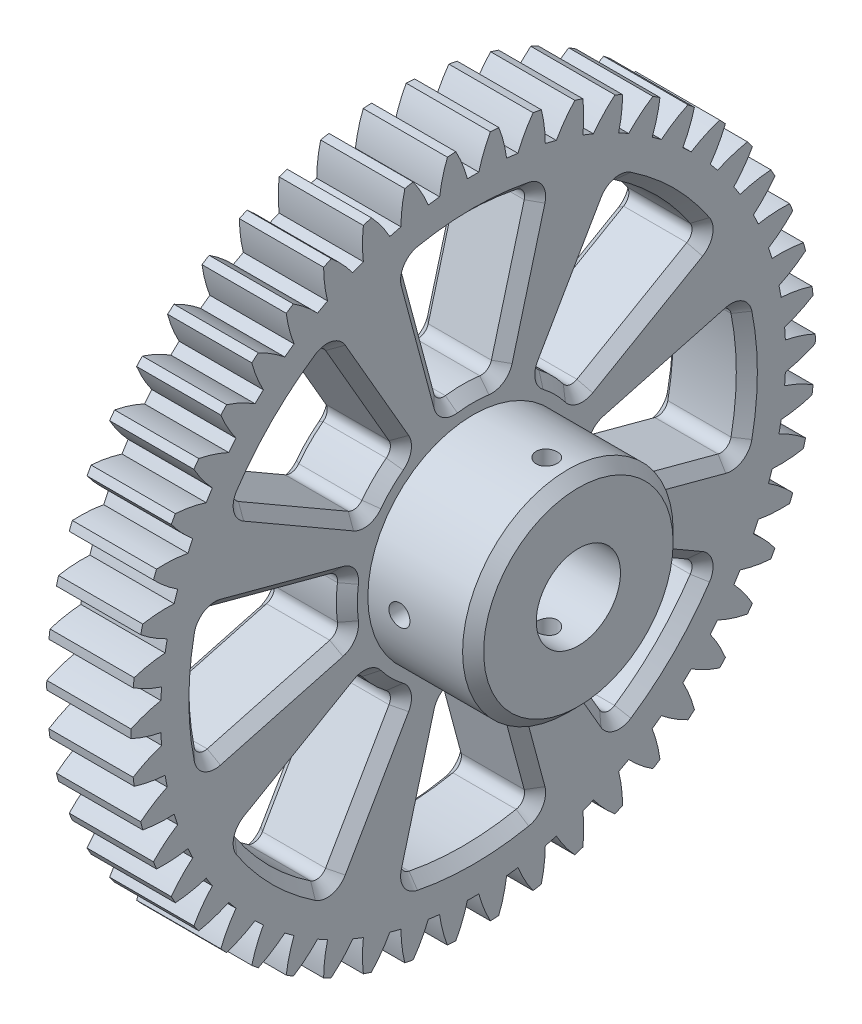
SolidWorks part; units mm, degrees
material "ПК/АБС"
ref_plane "Plane1" through (0, 0, 0) normal (0, 0, 1) x (1, 0, 0)
ref_plane "Plane2" through (0, 0, 0) normal (0, 1, 0) x (1, 0, 0)
ref_plane "Plane3" through (0, 0, 0) normal (1, 0, 0) x (0, 0, -1)
sketch "HoldingSke" plane through (0, 0, 0) normal (0, 1, 0) x (1, 0, 0)
  line L0 (0, 0) -> (0.5142, -0.6128)
  line L1 (-15, 0) -> (100, 0) construction
  line L2 (0, 0) -> (-2.1039, 2.3779)
  line L3 (0, 0) -> (-11.863, 4.5341)
  line L4 (0, 0) -> (5.5511, 6.6156)
  line L5 (0, 0) -> (-46.8476, -17.4728)
  line L6 (0, 0) -> (-6.6317, -4.4744)
  line L7 (-2.1039, 2.3779) -> (8.6587, 51.2063)
  line L8 (-76.2, 54.61) -> (-74.8, 54.61)
  line L9 (-71.009, 38.7566) -> (-53.1078, 45.2721)
  line L10 (-76.2, 71.12) -> (104.1128, 71.12)
  line L11 (0, 0) -> (-8, 0)
  line L12 (-76.2, 101.6) -> (-76.155, 101.6)
  line L13 (24.9733, 27.94) -> (52.9518, 28.4284)
  line L14 (24.9733, 27.94) -> (24.9743, 27.94)
  line L15 (24.9733, 27.94) -> (100.4006, 29.5858)
  line L16 (-63.627, -1.25) -> (-12.827, -1.25)
  circle A0 centre (0, 0) radius 4
  circle A1 centre (0, 0) radius 29.6865
  circle A2 centre (0, 0) radius 37.5
  circle A3 centre (0, 0) radius 4
  dimension "MHD" = 59.373
  dimension "Hub_dia" = 75
  dimension "Bore" = 8
  dimension "MBD" = 8
  dimension "Num_teeth" = 50
  dimension "Pitch" = 0.8
  dimension "Overall_len" = 50
  dimension "Show_teeth" = 50
  dimension "Thickness" = 8
  dimension "OAL" = 50.0005
  dimension "T_dim" = 1.4
  dimension "Ap" = 20
  dimension "H" = 19.05
  dimension "Pitch_radius" = 180.3128
  dimension "Width" = 8
  dimension "Backlash" = 0.045
  dimension "Addendum_fac" = 1
  dimension "Dedendum_fac" = 1.25
  dimension "Clearance_fac" = 0.25
  dimension "Dedendum_add" = 0.001
  dimension "Module" = 1.25
sketch "BasProSke" plane through (0, 0, 0) normal (0, 1, 0) x (1, 0, 0)
  line L0 (-10, 0) -> (60, 0) construction
  line L1 (0, 0) -> (0, 32.5)
  line L2 (0, 0) -> (8, 0)
  line L3 (8, 0) -> (8, 32.5)
  line L4 (8, 32.5) -> (0, 32.5)
  dimension "Thickness" = 8
  dimension "Diameter" = 65
revolve "Base-Revolve" add sketch "BasProSke" angle 360 about L0
sketch "TooCutSke" plane through (0, 0, 0) normal (1, 0, 0) x (0, 0, -1)
  line L1 (0, 0) -> (0, 107) construction
  line L2 (0, 0) -> (-1.0603, 31.232) construction
  line L3 (0, 0) -> (-3.9228, 62.3506) construction
  line L4 (-1.0603, 31.232) -> (-1.9614, 31.1753) construction
  arc A0 (0.543, 29.6815) -> (-0.543, 29.6815) centre (0, 0) ccw
  arc A1 (1.6539, 32.4833) -> (-1.6539, 32.4833) centre (0, 0) ccw
  circle A2 centre (0, 0) radius 31.25 construction
  circle A3 centre (0, 0) radius 29.3654 construction
  arc A4 (-0.543, 29.6815) -> (-1.6539, 32.4833) centre (-12.6336, 26.5088) ccw
  arc A5 (1.6539, 32.4833) -> (0.543, 29.6815) centre (12.6336, 26.5088) ccw
  dimension "Root_dia" = 59.373
  dimension "Overcut_dia" = 65.0508
  dimension "Pitch_dia" = 62.5
  dimension "Base_dia" = 58.7308
  dimension "Flank_rad" = 12.5
  dimension "Half_ang" = 3.6
  dimension "Half_CT" = 0.9028
extrude "ToothCut" cut sketch "TooCutSke" along normal through all
fillet "Breaks" [suppressed] radius 0.025
fillet "RootFillets" [suppressed] radius 0.3135
pattern_circular "TeethCuts" count 50 every 7.2 about axis through (-10, 0, 0) along (1, 0, 0) of "ToothCut", "RootFillets", "Breaks"
sketch "HubNeaOneSke" plane through (0, 0, 0) normal (-1, 0, 0) x (0, 0, 1)
  circle A0 centre (0, 0) radius 29.6865
  dimension "Diameter" = 59.373
extrude "HubNearOne" [suppressed] add sketch "HubNeaOneSke" along normal blind 42.0005
sketch "HubNeaBotSke" plane through (0, 0, 0) normal (-1, 0, 0) x (0, 0, 1)
  circle A0 centre (0, 0) radius 29.6865
  dimension "Diameter" = 59.373
extrude "HubNearBoth" [suppressed] add sketch "HubNeaBotSke" along normal blind 21.0002
ref_plane "FarPln" through (8, 0, 0) normal (1, 0, 0) x (0, 0, -1)
sketch "HubFarSke" plane through (8, 0, 0) normal (1, 0, 0) x (0, 0, -1)
  circle A0 centre (0, 0) radius 29.6865
  dimension "Diameter" = 59.373
extrude "HubFar" [suppressed] add sketch "HubFarSke" along normal blind 21.0002
sketch "BorSke" plane through (0, 0, 0) normal (1, 0, 0) x (0, 0, -1)
  circle A0 centre (0, 0) radius 4
  dimension "Diameter" = 8
extrude "Bore" cut sketch "BorSke" along normal mid plane 100.0009
sketch "KeySke" plane through (0, 0, 0) normal (1, 0, 0) x (0, 0, -1)
  line L0 (-1.5, 0) -> (-1.5, 5.4)
  line L1 (-1.5, 5.4) -> (1.5, 5.4)
  line L2 (1.5, 5.4) -> (1.5, 0)
  line L3 (0, 0) -> (0, 34) construction
  line L4 (-1.5, 0) -> (1.5, 0)
  dimension "Offset" = 5.4
  dimension "Width" = 3
extrude "Keyway" [suppressed] cut sketch "KeySke" along normal mid plane 100.0009
pattern_circular "Keyway2" [suppressed] count 2 every 90 about axis through (-10, 0, 0) along (1, 0, 0)
sketch "Эскиз1" plane through (8, 0, 0) normal (1, 0, 0) x (0, 0, -1)
  circle A0 centre (0, 0) radius 4 construction
  circle A1 centre (0, 0) radius 4
  circle A2 centre (0, 0) radius 10
  dimension "D1" = 20
extrude "Бобышка-Вытянуть1" add sketch "Эскиз1" along normal blind 10
sketch "Эскиз2" plane through (0, 0, 0) normal (0, 1, 0) x (1, 0, 0)
  line L0 (18, -10) -> (18, 10) construction
  line L1 (18, -10) -> (18, 10)
  line L2 (8, -10) -> (8, 10) construction
  line L3 (8, -10) -> (8, 10)
  line L4 (18, 0) -> (8, 0) construction
  circle A0 centre (15, 0) radius 1
  dimension "D1" = 2
  dimension "D2" = 3
extrude "Вырез-Вытянуть1" cut sketch "Эскиз2" against normal through all both and the other way through all contours A0 L4 | L4 A0
sketch "Эскиз3" plane through (0, 0, 0) normal (0, 0, 1) x (1, 0, 0)
  line L0 (18, -10) -> (18, 10) construction
  line L1 (18, -10) -> (18, 10)
  line L2 (8, -10) -> (8, 10) construction
  line L3 (8, -10) -> (8, 10)
  line L4 (18, 0) -> (8, 0) construction
  circle A0 centre (11, 0) radius 1
  dimension "D1" = 2
  dimension "D2" = 3
extrude "Вырез-Вытянуть2" cut sketch "Эскиз3" against normal through all both and the other way through all contours L4 A0 | A0 L4
chamfer "Фаска1" distance 1 angle 45 1 edges at (18, 0, -10)
chamfer "Фаска2" distance 1 angle 45 1 edges at (0, 0, -4)
sketch "Эскиз4" plane through (8, 0, 0) normal (1, 0, 0) x (0, 0, -1)
  line L0 (-39.9819, 0) -> (39.9819, 0) construction
  line L1 (-11.7367, -2.5) -> (-25.2681, -6.1257)
  line L2 (-11.7367, 2.5) -> (-25.2681, 6.1257)
  circle A0 centre (0, 0) radius 10 construction
  circle A1 centre (0, 0) radius 10
  circle A2 centre (0, 0) radius 12
  circle A3 centre (0, 0) radius 26
  dimension "D1" = 52
  dimension "D2" = 24
  dimension "D3" = 30
  dimension "D4" = 5
extrude "Вырез-Вытянуть3" cut sketch "Эскиз4" against normal through all both and the other way through all contours A3 L0 A2 L2 | L0 A3 L1 A2
fillet "Скругление1" radius 1 4 edges at (4, 2.5, 11.7367) (4, -2.5, 11.7367) (4, 6.1257, 25.2681) (4, -6.1257, 25.2681)
chamfer "Фаска3" distance 1 angle 45 16 edges at (0, -4.2959, 18.4392) (0, -2.3239, 12.0458) (0, -5.7386, 25.0451) (0, 0, 12) (0, 0, 26) (0, 2.3239, 12.0458) (0, 5.7386, 25.0451) (0, 4.2959, 18.4392) (8, 0, 12) (8, -2.3239, 12.0458) (8, 2.3239, 12.0458) (8, -4.2959, 18.4392) (8, 4.2959, 18.4392) (8, -5.7386, 25.0451) (8, 5.7386, 25.0451) (8, 0, 26)
pattern_circular "Круговой массив1" count 8 every 45 about axis through (0, 0, 0) along (1, 0, 0) of "Вырез-Вытянуть3", "Скругление1", "Фаска3"
equation "' \"Module@HoldingSke\" = 6.35"
equation "' \"Num_teeth@HoldingSke\" = 12"
equation "' \"Ap@HoldingSke\" =  20"
equation "' \"Ap@HoldingSke\" = 20"
equation "' \"Width@HoldingSke\" = 0.5 * 25.4"
equation "' \"Hub_dia@HoldingSke\"= 1 * 25.4"
equation "' \"Hub_dia@HoldingSke\" = 1 * 25.4"
equation "' \"Overall_len@HoldingSke\" = 1.0 * 25.4"
equation "' \"Bore@HoldingSke\" = 0.75 * 25.4"
equation "' \"T_dim@HoldingSke\" = 0.1 * 25.4"
equation "' \"Width@KeySke\" = 0.25 * 25.4"
equation "' \"Show_teeth@HoldingSke\" = 13"
equation "' \"Backlash@HoldingSke\" = 0.009 * 25.4"
equation "' \"Addendum_fac@HoldingSke\" = 1.0"
equation "' \"Dedendum_fac@HoldingSke\" = 1.25"
equation "' \"Dedendum_add@HoldingSke\" = 0.00005 * 25.4"
equation "' \"Clearance_fac@HoldingSke\" = 0.25"
equation "\"Pitch@HoldingSke\" = 1 / \"Module@HoldingSke\""
equation "\"Overcut_dia@TooCutSke\" = (\"Num_teeth@HoldingSke\" + 2 * \"Addendum_fac@HoldingSke\") / \"Pitch@HoldingSke\" + 0.002 * 25.4"
equation "\"Pitch_dia@TooCutSke\" = \"Num_teeth@HoldingSke\" / \"Pitch@HoldingSke\""
equation "\"Base_dia@TooCutSke\" = \"Num_teeth@HoldingSke\" / \"Pitch@HoldingSke\" * cos((\"Ap@HoldingSke\"  * 3.14159265 / 180))"
equation "\"Root_dia@TooCutSke\" = (\"Num_teeth@HoldingSke\" + 2) / \"Pitch@HoldingSke\" - 2 * (\"Addendum_fac@HoldingSke\" + \"Dedendum_fac@HoldingSke\") / \"Pitch@HoldingSke\" - \"Dedendum_add@HoldingSke\" * 2"
equation "\"Half_ang@TooCutSke\" = 180 / \"Num_teeth@HoldingSke\""
equation "\"Half_CT@TooCutSke\" = \"Num_teeth@HoldingSke\" / \"Pitch@HoldingSke\" * sin((3.14159265 / 2 / \"Num_teeth@HoldingSke\")) / 2 - 7 * \"Backlash@HoldingSke\" / 4"
equation "\"Flank_rad@TooCutSke\" = \"Num_teeth@HoldingSke\" / \"Pitch@HoldingSke\" / 5"
equation "\"Radius@RootFillets\" = \"Clearance_fac@HoldingSke\" / \"Pitch@HoldingSke\" + \"Dedendum_add@HoldingSke\""
equation "\"Break_rad@Breaks\" = 0.02 / \"Pitch@HoldingSke\""
equation "\"Thickness@HoldingSke\" = \"Width@HoldingSke\""
equation "\"OAL@HoldingSke\" = \"Thickness@HoldingSke\""
equation "\"MHD@HoldingSke\" = (\"Num_teeth@HoldingSke\" + 2) / \"Pitch@HoldingSke\" - 2 * (\"Addendum_fac@HoldingSke\" + \"Dedendum_fac@HoldingSke\")  / \"Pitch@HoldingSke\" - \"Dedendum_add@HoldingSke\" * 2"
equation "\"MBD@HoldingSke\" = (\"Num_teeth@HoldingSke\" + 2) / \"Pitch@HoldingSke\" - 2 * (\"Addendum_fac@HoldingSke\" + \"Dedendum_fac@HoldingSke\")  / \"Pitch@HoldingSke\" - \"Dedendum_add@HoldingSke\" * 2 - 0.002 * 25.4"
equation "\"MHD@HoldingSke\" = ((sgn( \"MHD@HoldingSke\" - \"Hub_dia@HoldingSke\" )-1)*( \"MHD@HoldingSke\" - \"Hub_dia@HoldingSke\" ))/-2+ \"Hub_dia@HoldingSke\""
equation "\"MBD@HoldingSke\" = ((sgn( \"MBD@HoldingSke\" - \"Bore@HoldingSke\" )-1)*( \"MBD@HoldingSke\" - \"Bore@HoldingSke\" ))/-2+ \"Bore@HoldingSke\""
equation "\"OAL@HoldingSke\" = ((sgn( \"OAL@HoldingSke\" - \"Overall_len@HoldingSke\" )+1)*( \"OAL@HoldingSke\" - \"Overall_len@HoldingSke\" ))/2 + \"Overall_len@HoldingSke\" + 0.000002 * 25.4"
equation "\"Num_teeth@TeethCuts\" = int( \"Show_teeth@HoldingSke\" ) + 1"
equation "\"Num_teeth@TeethCuts\" = ((sgn( \"Num_teeth@TeethCuts\" - \"Num_teeth@HoldingSke\" )-1)*( \"Num_teeth@TeethCuts\" - \"Num_teeth@HoldingSke\" ))/-2+ \"Num_teeth@HoldingSke\""
equation "\"Num_teeth@TeethCuts\" = ((sgn( \"Num_teeth@TeethCuts\" - 2.0)+1)*( \"Num_teeth@TeethCuts\" - 2.0))/2 +2.0"
equation "\"Angle@TeethCuts\" = 360.0 / \"Num_teeth@HoldingSke\""
equation "\"Diameter@BasProSke\" = (\"Num_teeth@HoldingSke\" + 2 * \"Addendum_fac@HoldingSke\") / \"Pitch@HoldingSke\""
equation "\"Thickness@BasProSke\"  = \"Thickness@HoldingSke\""
equation "' \"Fillet_rad@BasProSke\" =  \"Thickness@HoldingSke\" * 0.05"
equation "' \"Fillet_rad@BasProSke\" = \"Thickness@HoldingSke\" * 0.05"
equation "\"MHD@HoldingSke\" = ((sgn( \"MHD@HoldingSke\" - \"Root_dia@TooCutSke\" )-1)*( \"MHD@HoldingSke\" - \"Root_dia@TooCutSke\" ))/-2+ \"Root_dia@TooCutSke\""
equation "\"Diameter@HubNeaOneSke\" = \"MHD@HoldingSke\""
equation "\"Length@HubNearOne\" = \"OAL@HoldingSke\" - \"Thickness@BasProSke\""
equation "\"Diameter@HubNeaBotSke\" = \"MHD@HoldingSke\""
equation "\"Length@HubNearBoth\" = ( \"OAL@HoldingSke\" - \"Thickness@BasProSke\" ) / 2.0"
equation "\"Thickness@FarPln\" = \"Thickness@BasProSke\""
equation "\"Diameter@HubFarSke\" = \"MHD@HoldingSke\""
equation "\"Length@HubFar\" = ( \"OAL@HoldingSke\" - \"Thickness@BasProSke\" ) / 2.0"
equation "\"Diameter@BorSke\" = \"MBD@HoldingSke\""
equation "\"D1@Bore\" = \"OAL@HoldingSke\" * 2.0"
equation "\"D1@Keyway\" = \"OAL@HoldingSke\" * 2.0"
equation "\"Offset@KeySke\" = \"T_dim@HoldingSke\" + \"MBD@HoldingSke\" / 2.0"
